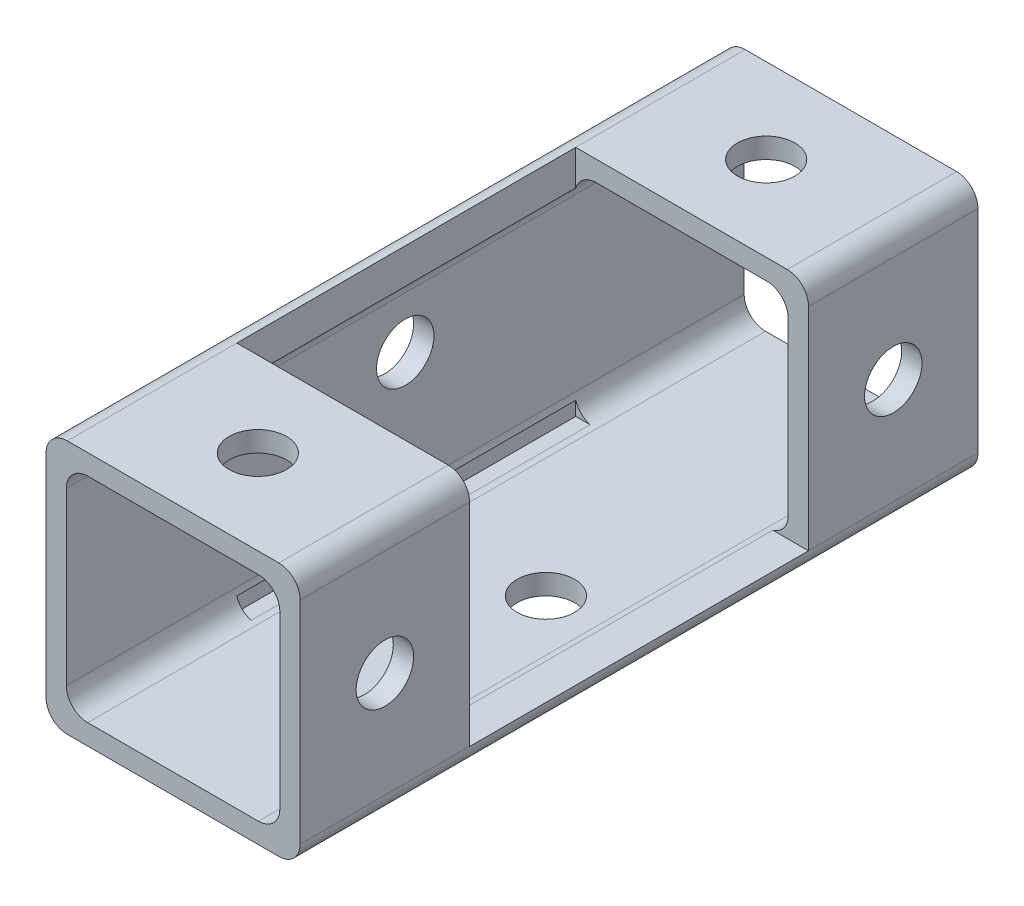
SolidWorks part; units mm, degrees
material "6061-T6 (SS)"
ref_plane "Front Plane" through (0, 0, 0) normal (0, 0, 1) x (1, 0, 0)
ref_plane "Top Plane" through (0, 0, 0) normal (0, 1, 0) x (1, 0, 0)
ref_plane "Right Plane" through (0, 0, 0) normal (1, 0, 0) x (0, 0, -1)
sketch "Sketch1" plane through (0, 0, 0) normal (0, 0, 1) x (1, 0, 0)
  line L0 (9.525, 0) -> (8.001, 0) construction
  line L1 (-9.525, 0) -> (9.525, 0) construction
  line L2 (0, 9.525) -> (0, -9.525)
  point P7 (0, 0)
sketch "Sketch2" plane through (0, 0, 0) normal (1, 0, 0) x (0, 0, -1)
  line L0 (25.4, 0) -> (-25.4, 0)
  point P4 (0, 0)
  dimension "Length" = 50.8
sketch "Sketch3" plane through (0, 0, 0) normal (0, 0, 1) x (1, 0, 0)
  line L5 (-8.001, -8.001) -> (8.001, -8.001)
  line L6 (-8.001, -8.001) -> (-8.001, 8.001)
  line L11 (-8.001, 8.001) -> (8.001, 8.001)
  line L12 (8.001, -8.001) -> (8.001, 8.001)
  line L14 (-8.001, -8.001) -> (8.001, 8.001) construction
  line L15 (-8.001, 8.001) -> (8.001, -8.001) construction
  line L16 (-9.525, -9.525) -> (9.525, -9.525)
  line L17 (-9.525, -9.525) -> (-9.525, 9.525)
  line L18 (-9.525, 9.525) -> (9.525, 9.525)
  line L19 (9.525, -9.525) -> (9.525, 9.525)
  line L20 (-9.525, -9.525) -> (9.525, 9.525) construction
  line L21 (-9.525, 9.525) -> (9.525, -9.525) construction
  point P0 (0, 0)
  point P5 (0, 0)
  point P10 (8.001, -9.525)
  dimension "D2" = 1.524
  dimension "D3" = 19.05
  dimension "D4" = 19.05
  dimension "D1" = 1.524
extrude "Boss-Extrude1" add sketch "Sketch3" along normal up to vertex (25.4 mm away) and the other way up to vertex (25.4 mm away) up to point (0, 0, 25.4) other way up to point (0, 0, -25.4)
fillet "Fillet1" radius 1.6002 8 edges at (-8.001, -8.001, 0) (8.001, -8.001, 0) (-8.001, 8.001, 0) (8.001, 8.001, 0) (-9.525, -9.525, 0) (9.525, -9.525, 0) (-9.525, 9.525, 0) (9.525, 9.525, 0)
sketch "Sketch4" plane through (0, 0, 0) normal (1, 0, 0) x (0, 0, -1)
  line L0 (25.4, 0) -> (-25.4, 0) construction
  line L1 (-25.4, -7.9248) -> (-25.4, 7.9248) construction
  line L2 (25.4, -7.9248) -> (25.4, 7.9248) construction
  point P0 (-3.9687, 0)
  point P6 (0, 0)
  point P8 (3.175, 0)
  point P9 (-3.175, 0)
  point P10 (3.9687, 0)
  dimension "D1" = 21.4312
  dimension "D2" = 28.575
  dimension "D3" = 21.4312
  dimension "D4" = 28.575
sketch "Sketch5" plane through (0, 9.525, 0) normal (0, 1, 0) x (1, 0, 0)
  line L0 (0, 25.4) -> (0, -25.4) construction
  line L1 (7.9248, 25.4) -> (-7.9248, 25.4) construction
  line L2 (7.9248, -25.4) -> (-7.9248, -25.4) construction
  line L3 (-7.9248, 25.4) -> (-7.9248, -25.4) construction
  line L4 (-7.9248, -12.7) -> (11.8601, -12.7)
  line L5 (-7.9248, -12.7) -> (-7.9248, 12.7)
  line L6 (-7.9248, 12.7) -> (11.8601, 12.7)
  line L7 (11.8601, -12.7) -> (11.8601, 12.7)
  point P6 (0, 0)
  point P13 (-7.9248, 0)
  dimension "D1" = 25.4
extrude "Cut-Extrude1" cut sketch "Sketch5" against normal blind 17.4625
sketch "Sketch6" plane through (0, -8.001, 0) normal (0, 1, 0) x (1, 0, 0)
  line L0 (-7.9248, 12.7) -> (-7.9248, -12.7) construction
  circle A0 centre (2.54, 0) radius 2.1527
  dimension "D1" = 4.3053
  dimension "D2" = 10.4648
sketch "Sketch7" plane through (0, 9.525, 0) normal (0, 1, 0) x (1, 0, 0)
  line L0 (0, 25.4) -> (0, 12.7) construction
  line L1 (7.9248, 25.4) -> (-7.9248, 25.4) construction
  line L2 (7.9248, 12.7) -> (-7.9248, 12.7) construction
  line L3 (0, 12.7) -> (0, -12.7) construction
  line L4 (-7.9248, -12.7) -> (7.9248, -12.7) construction
  line L5 (0, -12.7) -> (0, -25.4) construction
  line L6 (7.9248, -25.4) -> (-7.9248, -25.4) construction
  circle A0 centre (0, 19.05) radius 2.1526
  circle A1 centre (2.54, 0) radius 2.1526
  circle A2 centre (0, -19.05) radius 2.1526
  dimension "D1" = 4.3053
  dimension "D2" = 2.54
extrude "Cut-Extrude2" cut sketch "Sketch7" against normal blind 12.7 contours A1 | A0 | A2
extrude "Cut-Extrude3" cut sketch "Sketch6" against normal through all contours A0
sketch "Sketch9" plane through (9.525, 0, 0) normal (1, 0, 0) x (0, 0, -1)
  line L0 (-25.4, 0) -> (-12.7, 0) construction
  line L1 (-25.4, -7.9248) -> (-25.4, 7.9248) construction
  line L2 (-12.7, -7.9248) -> (-12.7, 7.9248) construction
  line L3 (-12.7, 0) -> (12.7, 0) construction
  line L4 (12.7, 7.9248) -> (12.7, -7.9248) construction
  line L5 (12.7, 0) -> (25.4, 0) construction
  line L6 (25.4, -7.9248) -> (25.4, 7.9248) construction
  circle A0 centre (-19.05, 0) radius 2.1527
  circle A1 centre (19.05, 0) radius 2.1527
  dimension "D1" = 4.3053
extrude "Cut-Extrude5" cut sketch "Sketch9" against normal blind 6.35
sketch "Sketch10" plane through (9.525, 0, 0) normal (1, 0, 0) x (0, 0, -1)
  line L0 (-12.7, 0) -> (12.7, 0) construction
  line L1 (-12.7, -7.9248) -> (-12.7, 7.9248) construction
  line L2 (12.7, 7.9248) -> (12.7, -7.9248) construction
  line L3 (0, 0) -> (0, 4.8211) construction
  circle A0 centre (0, 2.54) radius 2.1526
  dimension "D1" = 4.3053
  dimension "D2" = 2.54
extrude "Cut-Extrude6" cut sketch "Sketch10" against normal through all
equation "\"D2@Sketch3\"=\"Wall Thickness@Sketch1\""
equation "\"D1@Sketch4\"=\"Width@Sketch1\"*1.125"
equation "\"D2@Sketch4\"=\"Width@Sketch1\"*1.5"
equation "\"D3@Sketch4\"=\"D1@Sketch4\""
equation "\"D4@Sketch4\"=\"D2@Sketch4\""
